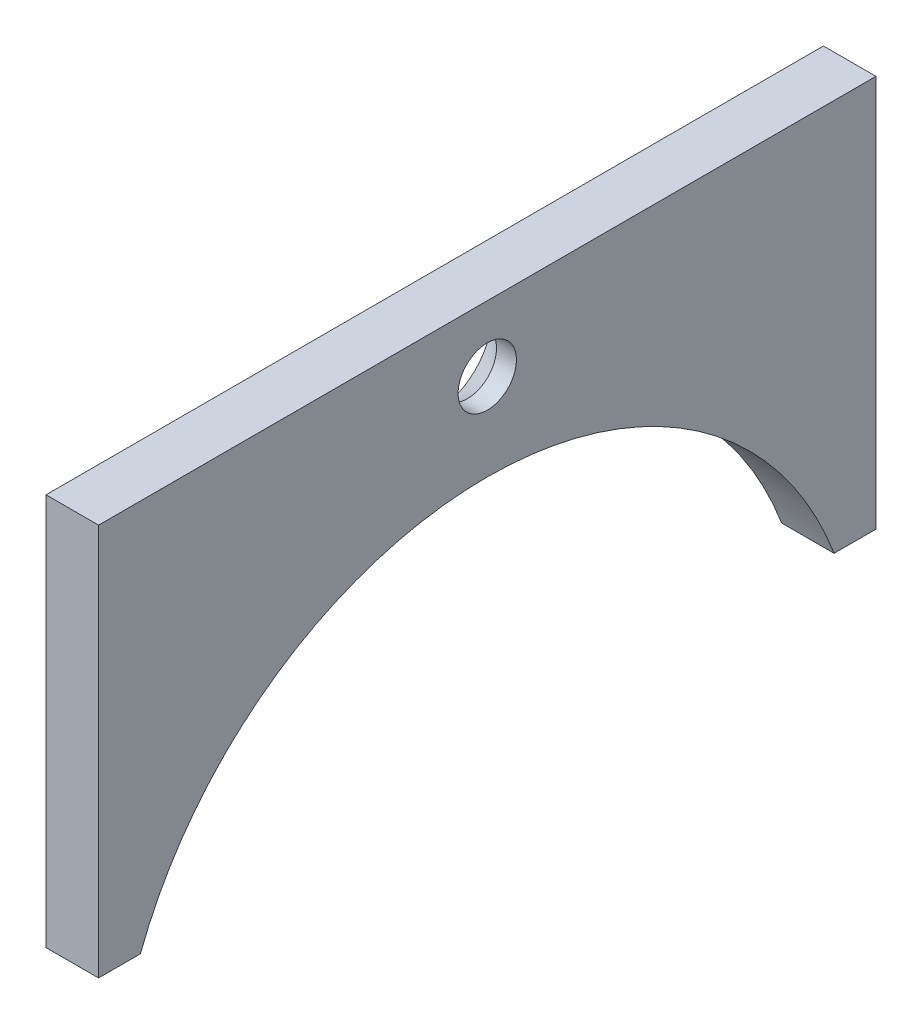
SolidWorks part; units mm, degrees
material "6061-T4 (SS)"
ref_plane "Front Plane" through (0, 0, 0) normal (0, 0, 1) x (1, 0, 0)
ref_plane "Top Plane" through (0, 0, 0) normal (0, 1, 0) x (1, 0, 0)
ref_plane "Right Plane" through (0, 0, 0) normal (1, 0, 0) x (0, 0, -1)
sketch "Sketch1" plane through (0, 0, 0) normal (0, 0, 1) x (1, 0, 0)
  line L1 (-3.3502, 4) -> (-1.75, 4)
  line L2 (-3.3502, 4) -> (-3.3502, 15.95)
  line L3 (-3.3502, 15.95) -> (-1.75, 15.95)
  line L4 (-1.75, 4) -> (-1.75, 15.95)
extrude "Boss-Extrude1" add sketch "Sketch1" along normal up to surface (23.6854 mm away)
sketch "Sketch2" plane through (-1.75, 0, 0) normal (1, 0, 0) x (0, 0, -1)
  line L0 (-23.6854, 4) -> (0, 4) construction
  line L1 (-22.4111, 4) -> (-1.2744, 4)
  arc A0 (-1.2744, 4) -> (-22.4111, 4) centre (-11.8427, 0) ccw
  arc A1 (-1.2744, 4) -> (-22.4111, 4) centre (-11.8427, 0) ccw construction
extrude "Cut-Extrude1" cut sketch "Sketch2" against normal blind 10
sketch "Sketch3" plane through (-1.75, 0, 0) normal (1, 0, 0) x (0, 0, -1)
  point P0 (-11.8427, 13.95)
  point P1 (-11.8427, 14.225)
  point P3 (-11.8427, 13.95)
hole_wizard "CSK for #0 Flat Head Socket Cap Screw1" positions "Sketch4" profile "Sketch5" countersink size "#0" standard "ANSI Inch"
sketch "Sketch4" plane through (-3.3502, 0, 0) normal (-1, 0, 0) x (0, 0, 1)
  point P0 (11.8427, 13.95)
sketch "Sketch5" plane through (-3.3502, 13.95, 11.8427) normal (0, 1, 0) x (0, 0, 1)
  line L0 (0, 0) -> (0, 3.5342)
  line L1 (0, 3.5342) -> (0.889, 3)
  line L2 (0.889, 3) -> (0.889, 0.9935)
  line L3 (0.889, 0.9935) -> (1.7526, 0)
  line L5 (1.7526, 0) -> (0, 0)
  line L6 (-0.889, 0.9935) -> (-1.7526, 0) construction
  line L10 (0, 3.5342) -> (-0.889, 3) construction
  line L11 (0, -6.35) -> (0, 107.95) construction
  dimension "Hole Dia." = 1.778
  dimension "Hole Depth" = 3
  dimension "Near C'Sink Dia." = 3.5052
  dimension "Near C'Sink Angle" = 82
  dimension "Drill Angle" = 118
